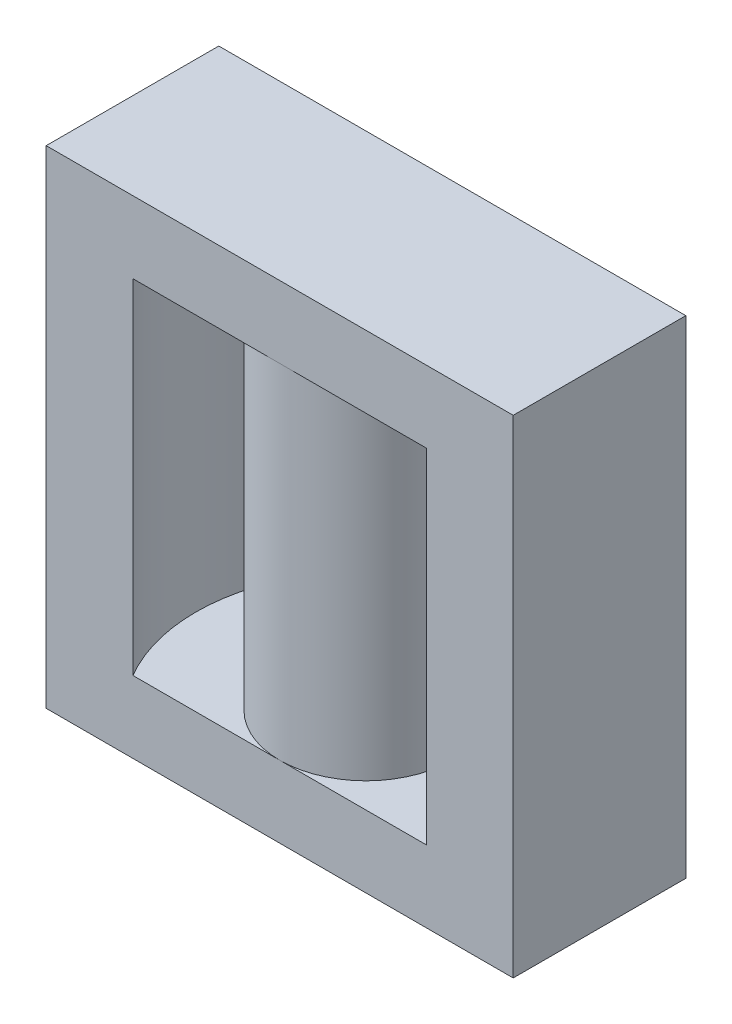
SolidWorks part; units mm, degrees
ref_plane "Front Plane" through (0, 0, 0) normal (0, 0, 1) x (1, 0, 0)
ref_plane "Top Plane" through (0, 0, 0) normal (0, 1, 0) x (1, 0, 0)
ref_plane "Right Plane" through (0, 0, 0) normal (1, 0, 0) x (0, 0, -1)
sketch "Sketch1" plane through (0, 0, 0) normal (0, 1, 0) x (1, 0, 0)
  line L1 (-29.9, 11.05) -> (29.9, 11.05)
  line L2 (-29.9, 11.05) -> (-29.9, -11.05)
  line L3 (-29.9, -11.05) -> (29.9, -11.05)
  line L4 (29.9, 11.05) -> (29.9, -11.05)
  circle A0 centre (0, 0) radius 11.05
  circle A1 centre (0, 0) radius 21.8
  dimension "D1" = 22.1
  dimension "D6" = 43.6
  dimension "D2" = 22.1
  dimension "D3" = 59.8
  dimension "D4" = 29.9
  dimension "D5" = 11.05
extrude "Boss-Extrude1" add sketch "Sketch1" along normal blind 62.4 contours A1 L1 L2 L3 | A0 | A1 L3 L4 L1
sketch "Sketch2" plane through (0, 62.4, 0) normal (0, 1, 0) x (1, 0, 0)
  line L1 (-29.9, 11.05) -> (29.9, 11.05)
  line L2 (-29.9, 11.05) -> (-29.9, -11.05)
  line L3 (-29.9, -11.05) -> (29.9, -11.05)
  line L4 (29.9, 11.05) -> (29.9, -11.05)
extrude "Boss-Extrude2" add sketch "Sketch2" against normal blind 9.2
sketch "Sketch3" plane through (0, 0, 0) normal (0, -1, 0) x (1, 0, 0)
  line L1 (-29.9, 11.05) -> (29.9, 11.05)
  line L2 (-29.9, 11.05) -> (-29.9, -11.05)
  line L3 (-29.9, -11.05) -> (29.9, -11.05)
  line L4 (29.9, 11.05) -> (29.9, -11.05)
extrude "Boss-Extrude3" add sketch "Sketch3" against normal blind 9.2
